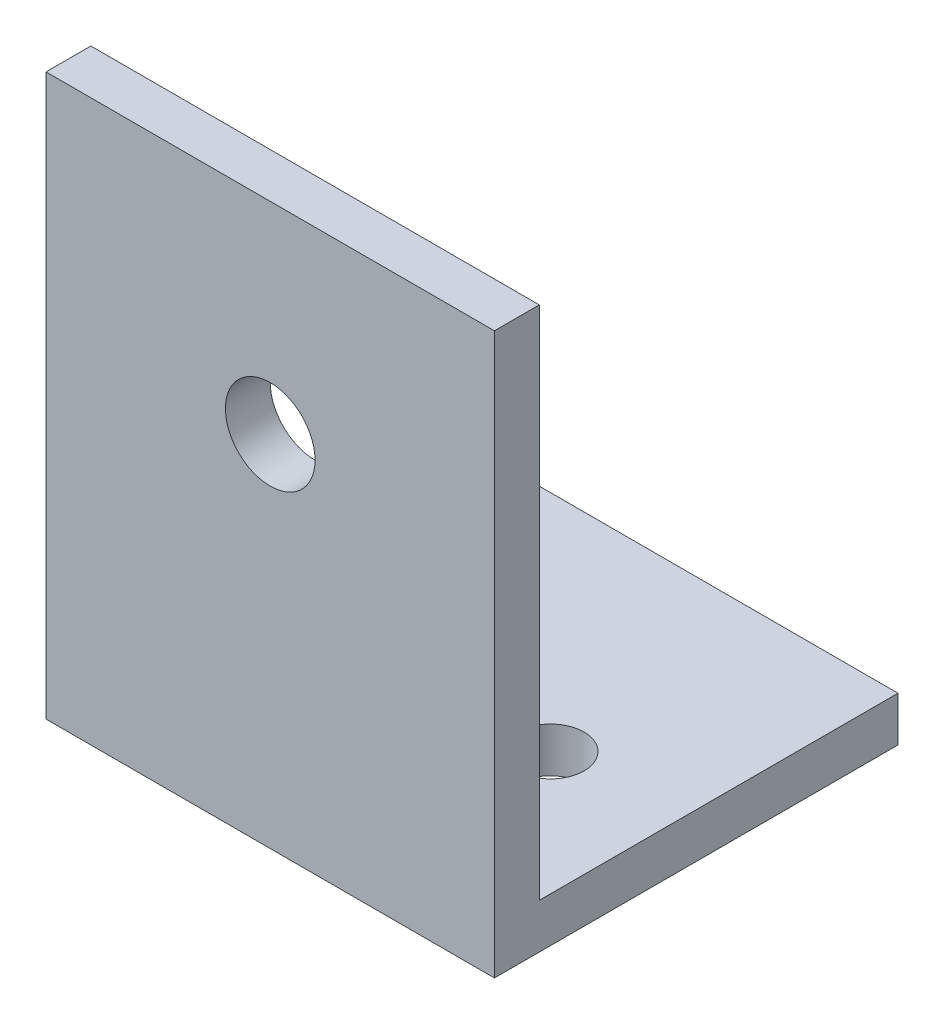
SolidWorks part; units mm, degrees
ref_plane "Front" through (0, 0, 0) normal (0, 0, 1) x (1, 0, 0)
ref_plane "Top" through (0, 0, 0) normal (0, 1, 0) x (1, 0, 0)
ref_plane "Right" through (0, 0, 0) normal (1, 0, 0) x (0, 0, -1)
sketch "草图1" plane through (0, 0, 0) normal (1, 0, 0) x (0, 0, -1)
  line L0 (0, 0) -> (0, 25)
  line L1 (0, 25) -> (3, 25)
  line L2 (3, 25) -> (3, 3)
  line L3 (3, 3) -> (18, 3)
  line L4 (18, 3) -> (18, 0)
  line L5 (18, 0) -> (0, 0)
  dimension "D1" = 25
  dimension "D2" = 3
  dimension "D3" = 22
  dimension "D4" = 15
extrude "凸台-拉伸1" add sketch "草图1" along normal blind 20
sketch "草图2" plane through (0, 3, 0) normal (0, 1, 0) x (1, 0, 0)
  line L0 (0, 8) -> (20, 8) construction
  line L1 (0, 18) -> (0, 3) construction
  line L2 (20, 18) -> (20, 3) construction
  line L3 (20, 0) -> (0, 0) construction
  circle A0 centre (5.5, 8) radius 1.5
  circle A1 centre (14.5, 8) radius 1.5
  dimension "D1" = 3
  dimension "D2" = 3
  dimension "D3" = 9
  dimension "D4" = 5.5
  dimension "D5" = 8
extrude "切除-拉伸1" cut sketch "草图2" against normal through all
sketch "草图3" plane through (0, 0, 0) normal (0, 0, 1) x (1, 0, 0)
  line L0 (10, 25) -> (10, 0) construction
  line L1 (20, 25) -> (0, 25) construction
  line L2 (20, 0) -> (0, 0) construction
  circle A0 centre (10, 16) radius 2
  dimension "D1" = 4
  dimension "D2" = 16
extrude "切除-拉伸2" cut sketch "草图3" against normal through all
sketch "草图4" plane through (0, 3, 0) normal (0, 1, 0) x (1, 0, 0)
  line L0 (20, 18) -> (0, 18) construction
  line L1 (0, 18) -> (20, 18)
  line L2 (0, 18) -> (0, 3)
  line L3 (0, 3) -> (20, 3)
  line L4 (20, 18) -> (20, 3)
extrude "切除-拉伸3" cut sketch "草图4" against normal blind 1
sketch "草图5" plane through (0, 0, -3) normal (0, 0, -1) x (-1, 0, 0)
  line L1 (0, 25) -> (-20, 25)
  line L2 (0, 25) -> (0, 2)
  line L3 (0, 2) -> (-20, 2)
  line L4 (-20, 25) -> (-20, 2)
extrude "切除-拉伸4" cut sketch "草图5" against normal blind 1
